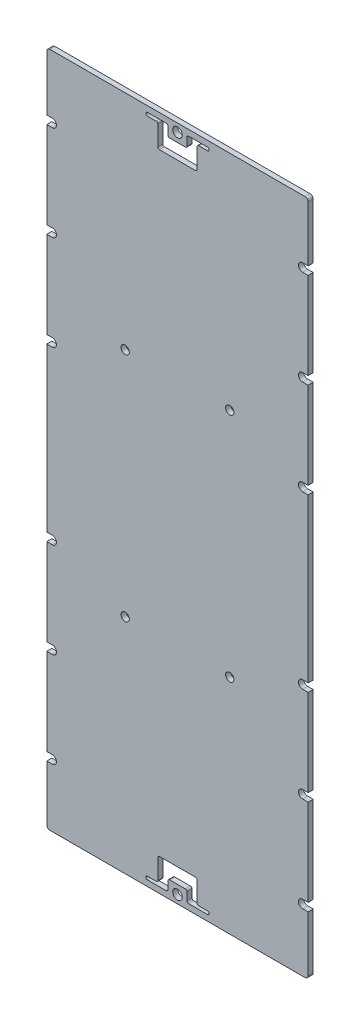
SolidWorks part; units mm, degrees
material "FR4_stuffedProtoboard"
ref_plane "Front Plane" through (0, 0, 0) normal (0, 0, 1) x (1, 0, 0)
ref_plane "Top Plane" through (0, 0, 0) normal (0, 1, 0) x (1, 0, 0)
ref_plane "Right Plane" through (0, 0, 0) normal (1, 0, 0) x (0, 0, -1)
sketch "Sketch1" plane through (0, 0, 0) normal (0, 0, 1) x (1, 0, 0)
  line L0 (-37, -97) -> (37, -97) construction
  line L5 (-37, -95.4) -> (37, -95.4) construction
  line L6 (-37, -87) -> (37, -87) construction
  line L7 (-37, -85.4) -> (37, -85.4) construction
  line L8 (-37, -77) -> (37, -77) construction
  line L9 (-37, -75.4) -> (37, -75.4) construction
  line L10 (-37, -67) -> (37, -67) construction
  line L11 (-37, -65.4) -> (37, -65.4) construction
  line L12 (-37, -57) -> (37, -57) construction
  line L13 (-37, -55.4) -> (37, -55.4) construction
  line L14 (-37, -47) -> (37, -47) construction
  line L15 (-37, -45.4) -> (37, -45.4) construction
  line L16 (-37, -37) -> (37, -37) construction
  line L17 (-37, -35.4) -> (37, -35.4) construction
  line L18 (-37, -27) -> (37, -27) construction
  line L19 (-37, -25.4) -> (37, -25.4) construction
  line L20 (-37, -17) -> (37, -17) construction
  line L21 (-37, -15.4) -> (37, -15.4) construction
  line L22 (-37, 15.4) -> (37, 15.4) construction
  line L23 (-37, 17) -> (37, 17) construction
  line L24 (-37, 25.4) -> (37, 25.4) construction
  line L25 (-37, 27) -> (37, 27) construction
  line L26 (-37, 35.4) -> (37, 35.4) construction
  line L27 (-37, 37) -> (37, 37) construction
  line L29 (-41.5, 107) -> (41.5, 107)
  line L30 (-41.5, 107) -> (-41.5, -107)
  line L31 (-41.5, -107) -> (41.5, -107)
  line L33 (41.5, 107) -> (41.5, -107)
  line L35 (-26.7, 107) -> (-28.3, 107) construction
  line L37 (-41.5, 109.5) -> (-41.5, 97.4) construction
  line L38 (41.5, 112.5) -> (41.5, 109.5) construction
  line L39 (-28.3, -107) -> (-26.7, -107) construction
  line L40 (-41.4, 106.9) -> (41.4, 106.9)
  line L41 (41.4, 106.9) -> (41.4, -106.9)
  line L42 (-41.4, -106.9) -> (41.4, -106.9)
  line L43 (-41.4, 106.9) -> (-41.4, -106.9)
  line L76 (-37, 45.4) -> (37, 45.4) construction
  line L77 (-37, 47) -> (37, 47) construction
  line L78 (-37, 55.4) -> (37, 55.4) construction
  line L79 (-37, 57) -> (37, 57) construction
  line L80 (-37, 65.4) -> (37, 65.4) construction
  line L81 (-37, 67) -> (37, 67) construction
  line L82 (-37, 75.4) -> (37, 75.4) construction
  line L83 (-37, 77) -> (37, 77) construction
  line L84 (-37, 85.4) -> (37, 85.4) construction
  line L85 (-37, 87) -> (37, 87) construction
  line L86 (-37, 95.4) -> (37, 95.4) construction
  line L87 (-37, 97) -> (37, 97) construction
  line L88 (-37, -97) -> (37, -97) construction
  line L89 (-37, -95.4) -> (37, -95.4) construction
  line L90 (-37, -87) -> (37, -87) construction
  line L91 (-37, -85.4) -> (37, -85.4) construction
  line L92 (-37, -77) -> (37, -77) construction
  line L93 (-37, -75.4) -> (37, -75.4) construction
  line L94 (-37, -67) -> (37, -67) construction
  line L95 (-37, -65.4) -> (37, -65.4) construction
  line L96 (-37, -57) -> (37, -57) construction
  line L97 (-37, -55.4) -> (37, -55.4) construction
  line L98 (-37, -47) -> (37, -47) construction
  line L99 (-37, -45.4) -> (37, -45.4) construction
  line L100 (-37, -37) -> (37, -37) construction
  line L101 (-37, -35.4) -> (37, -35.4) construction
  line L102 (-37, -27) -> (37, -27) construction
  line L103 (-37, -25.4) -> (37, -25.4) construction
  line L104 (-37, -17) -> (37, -17) construction
  line L105 (-37, -15.4) -> (37, -15.4) construction
  line L106 (-37, 15.4) -> (37, 15.4) construction
  line L107 (-37, 17) -> (37, 17) construction
  line L108 (-37, 25.4) -> (37, 25.4) construction
  line L109 (-37, 27) -> (37, 27) construction
  line L110 (-37, 35.4) -> (37, 35.4) construction
  line L111 (-37, 37) -> (37, 37) construction
  line L112 (-37, 45.4) -> (37, 45.4) construction
  line L113 (-37, 47) -> (37, 47) construction
  line L114 (-37, 55.4) -> (37, 55.4) construction
  line L115 (-37, 57) -> (37, 57) construction
  line L116 (-37, 65.4) -> (37, 65.4) construction
  line L117 (-37, 67) -> (37, 67) construction
  line L118 (-37, 75.4) -> (37, 75.4) construction
  line L119 (-37, 77) -> (37, 77) construction
  line L120 (-37, 85.4) -> (37, 85.4) construction
  line L121 (-37, 87) -> (37, 87) construction
  line L122 (-37, 95.4) -> (37, 95.4) construction
  line L123 (-37, 97) -> (37, 97) construction
  circle A0 centre (-39.5, 87) radius 0.8 construction
  circle A1 centre (-39.5, -27) radius 0.8 construction
  circle A2 centre (-39.5, 57) radius 0.8 construction
  circle A3 centre (39.5, -27) radius 0.8 construction
  circle A4 centre (-39.5, -27) radius 0.8
  circle A5 centre (-39.5, 27) radius 0.8 construction
  circle A6 centre (-16.5, 36.5) radius 0.8 construction
  circle A8 centre (39.5, -27) radius 0.8
  circle A9 centre (-16.5, -36.5) radius 0.8 construction
  circle A11 centre (-39.5, -57) radius 0.8 construction
  circle A13 centre (-39.5, -87) radius 0.8 construction
  circle A16 centre (0, -104.2) radius 0.8 construction
  circle A19 centre (39.5, -87) radius 0.8 construction
  circle A21 centre (39.5, -57) radius 0.8 construction
  circle A22 centre (16.5, -36.5) radius 0.8 construction
  circle A27 centre (39.5, 27) radius 0.8 construction
  circle A28 centre (16.5, 36.5) radius 0.8 construction
  circle A30 centre (39.5, 57) radius 0.8 construction
  circle A32 centre (39.5, 87) radius 0.8 construction
  circle A35 centre (0, 104.2) radius 0.8 construction
  circle A38 centre (-39.5, 87) radius 0.8
  circle A40 centre (-39.5, 57) radius 0.8
  circle A43 centre (-39.5, 27) radius 0.8
  circle A44 centre (-16.5, 36.5) radius 0.8
  circle A47 centre (-16.5, -36.5) radius 0.8
  circle A49 centre (-39.5, -57) radius 0.8
  circle A51 centre (-39.5, -87) radius 0.8
  circle A54 centre (0, -104.2) radius 0.8
  circle A57 centre (39.5, -87) radius 0.8
  circle A59 centre (39.5, -57) radius 0.8
  circle A60 centre (16.5, -36.5) radius 0.8
  circle A65 centre (39.5, 27) radius 0.8
  circle A66 centre (16.5, 36.5) radius 0.8
  circle A68 centre (39.5, 57) radius 0.8
  circle A70 centre (39.5, 87) radius 0.8
  circle A73 centre (0, 104.2) radius 0.8
  dimension "D1" = 0.1
extrude "pcb extrude" add sketch "Sketch1" along normal blind 1.6
sketch "Sketch7" plane through (0, 0, 1.6) normal (0, 0, 1) x (1, 0, 0)
  line L0 (-41.4, 106.9) -> (41.4, 106.9) construction
  line L1 (-41.25, 106.9) -> (-41.4, 106.9)
  line L2 (-41.25, 106.75) -> (-41.25, -106.75)
  line L3 (-41.25, -106.9) -> (-41.4, -106.9)
  line L4 (-41.4, 106.9) -> (-41.4, -106.9)
  line L5 (-41.4, -106.9) -> (41.4, -106.9) construction
  line L6 (-41.4, 106.9) -> (-41.4, -106.9) construction
  line L7 (0, -0.88) -> (0, 0.88) construction
  line L8 (41.25, -106.9) -> (41.4, -106.9)
  line L9 (41.4, 106.9) -> (41.4, -106.9)
  line L10 (41.25, 106.9) -> (41.4, 106.9)
  line L11 (41.25, 106.75) -> (41.25, -106.75)
  line L12 (0.88, 0) -> (-0.88, 0) construction
  line L13 (-41.25, -106.9) -> (41.25, -106.9)
  line L15 (-41.25, -106.75) -> (41.25, -106.75)
  line L17 (-41.25, 106.75) -> (41.25, 106.75)
  line L19 (-41.25, 106.9) -> (41.25, 106.9)
  dimension "D1" = 0.15
  dimension "D2" = 0.15
  dimension "D3" = 0.15
  dimension "D4" = 0.15
extrude "Offset Edges" cut sketch "Sketch7" against normal up to surface (1.6 mm away) up to face at (0.8, 104.2, 0)
sketch "connector locations" plane through (0, 0, 1.6) normal (0, 0, 1) x (1, 0, 0)
  line L0 (-37, 97) -> (37, 97) construction
  line L1 (-33.9182, 100.556) -> (-9.2802, 100.556)
  line L2 (-33.9182, 100.556) -> (-33.9182, 99.159)
  line L3 (-33.9182, 99.159) -> (-9.2802, 99.159)
  line L4 (-9.2802, 100.556) -> (-9.2802, 99.159)
  line L5 (-33.9182, 100.556) -> (-9.2802, 99.159) construction
  line L6 (-33.9182, 99.159) -> (-9.2802, 100.556) construction
  line L7 (-37, 87) -> (37, 87) construction
  line L8 (-33.9182, 90.556) -> (-22.0818, 90.556)
  line L9 (-33.9182, 90.556) -> (-33.9182, 89.159)
  line L10 (-33.9182, 89.159) -> (-22.0818, 89.159)
  line L11 (-22.0818, 90.556) -> (-22.0818, 89.159)
  line L12 (-33.9182, 90.556) -> (-22.0818, 89.159) construction
  line L13 (-33.9182, 89.159) -> (-22.0818, 90.556) construction
  line L14 (0, -0.88) -> (0, 0.88) construction
  line L15 (-12.319, 90.556) -> (12.319, 90.556)
  line L16 (-12.319, 90.556) -> (-12.319, 89.159)
  line L17 (-12.319, 89.159) -> (12.319, 89.159)
  line L18 (12.319, 90.556) -> (12.319, 89.159)
  line L19 (-12.319, 90.556) -> (12.319, 89.159) construction
  line L20 (-12.319, 89.159) -> (12.319, 90.556) construction
  line L21 (-37, -85.4) -> (37, -85.4) construction
  line L22 (-33.9182, -91.844) -> (-9.2802, -91.844)
  line L23 (-33.9182, -91.844) -> (-33.9182, -93.241)
  line L24 (-33.9182, -93.241) -> (-9.2802, -93.241)
  line L25 (-9.2802, -91.844) -> (-9.2802, -93.241)
  line L26 (-33.9182, -91.844) -> (-9.2802, -93.241) construction
  line L27 (-33.9182, -93.241) -> (-9.2802, -91.844) construction
  line L28 (-33.9182, -81.844) -> (-22.0818, -81.844)
  line L29 (-33.9182, -81.844) -> (-33.9182, -83.241)
  line L30 (-33.9182, -83.241) -> (-22.0818, -83.241)
  line L31 (-22.0818, -81.844) -> (-22.0818, -83.241)
  line L32 (-33.9182, -81.844) -> (-22.0818, -83.241) construction
  line L33 (-33.9182, -83.241) -> (-22.0818, -81.844) construction
  line L34 (-12.319, -81.844) -> (12.319, -81.844)
  line L35 (-12.319, -81.844) -> (-12.319, -83.241)
  line L36 (-12.319, -83.241) -> (12.319, -83.241)
  line L37 (12.319, -81.844) -> (12.319, -83.241)
  line L38 (-12.319, -81.844) -> (12.319, -83.241) construction
  line L39 (-12.319, -83.241) -> (12.319, -81.844) construction
  line L40 (-37, -95.4) -> (37, -95.4) construction
  line L41 (-33.9182, 80.556) -> (-33.9182, 79.159)
  line L42 (-33.9182, 80.556) -> (-22.0818, 80.556)
  line L43 (-22.0818, 80.556) -> (-22.0818, 79.159)
  line L44 (-33.9182, 79.159) -> (-22.0818, 79.159)
  line L45 (-33.9182, 80.556) -> (-22.0818, 79.159) construction
  line L46 (-33.9182, 79.159) -> (-22.0818, 80.556) construction
  line L47 (-12.319, 80.556) -> (-12.319, 79.159)
  line L48 (-12.319, 80.556) -> (12.319, 80.556)
  line L49 (12.319, 80.556) -> (12.319, 79.159)
  line L50 (-12.319, 79.159) -> (12.319, 79.159)
  line L51 (-12.319, 80.556) -> (12.319, 79.159) construction
  line L52 (-12.319, 79.159) -> (12.319, 80.556) construction
  line L53 (-33.9182, 70.556) -> (-33.9182, 69.159)
  line L54 (-33.9182, 70.556) -> (-22.0818, 70.556)
  line L55 (-22.0818, 70.556) -> (-22.0818, 69.159)
  line L56 (-33.9182, 69.159) -> (-22.0818, 69.159)
  line L57 (-33.9182, 70.556) -> (-22.0818, 69.159) construction
  line L58 (-33.9182, 69.159) -> (-22.0818, 70.556) construction
  line L59 (-12.319, 70.556) -> (-12.319, 69.159)
  line L60 (-12.319, 70.556) -> (12.319, 70.556)
  line L61 (12.319, 70.556) -> (12.319, 69.159)
  line L62 (-12.319, 69.159) -> (12.319, 69.159)
  line L63 (-12.319, 70.556) -> (12.319, 69.159) construction
  line L64 (-12.319, 69.159) -> (12.319, 70.556) construction
  line L65 (-33.9182, 60.556) -> (-33.9182, 59.159)
  line L66 (-33.9182, 60.556) -> (-22.0818, 60.556)
  line L67 (-22.0818, 60.556) -> (-22.0818, 59.159)
  line L68 (-33.9182, 59.159) -> (-22.0818, 59.159)
  line L69 (-33.9182, 60.556) -> (-22.0818, 59.159) construction
  line L70 (-33.9182, 59.159) -> (-22.0818, 60.556) construction
  line L71 (-12.319, 60.556) -> (-12.319, 59.159)
  line L72 (-12.319, 60.556) -> (12.319, 60.556)
  line L73 (12.319, 60.556) -> (12.319, 59.159)
  line L74 (-12.319, 59.159) -> (12.319, 59.159)
  line L75 (-12.319, 60.556) -> (12.319, 59.159) construction
  line L76 (-12.319, 59.159) -> (12.319, 60.556) construction
  line L77 (-33.9182, 50.556) -> (-33.9182, 49.159)
  line L78 (-33.9182, 50.556) -> (-22.0818, 50.556)
  line L79 (-22.0818, 50.556) -> (-22.0818, 49.159)
  line L80 (-33.9182, 49.159) -> (-22.0818, 49.159)
  line L81 (-33.9182, 50.556) -> (-22.0818, 49.159) construction
  line L82 (-33.9182, 49.159) -> (-22.0818, 50.556) construction
  line L83 (-12.319, 50.556) -> (-12.319, 49.159)
  line L84 (-12.319, 50.556) -> (12.319, 50.556)
  line L85 (12.319, 50.556) -> (12.319, 49.159)
  line L86 (-12.319, 49.159) -> (12.319, 49.159)
  line L87 (-12.319, 50.556) -> (12.319, 49.159) construction
  line L88 (-12.319, 49.159) -> (12.319, 50.556) construction
  line L89 (-33.9182, 40.556) -> (-33.9182, 39.159)
  line L90 (-33.9182, 40.556) -> (-22.0818, 40.556)
  line L91 (-22.0818, 40.556) -> (-22.0818, 39.159)
  line L92 (-33.9182, 39.159) -> (-22.0818, 39.159)
  line L93 (-33.9182, 40.556) -> (-22.0818, 39.159) construction
  line L94 (-33.9182, 39.159) -> (-22.0818, 40.556) construction
  line L95 (-12.319, 40.556) -> (-12.319, 39.159)
  line L96 (-12.319, 40.556) -> (12.319, 40.556)
  line L97 (12.319, 40.556) -> (12.319, 39.159)
  line L98 (-12.319, 39.159) -> (12.319, 39.159)
  line L99 (-12.319, 40.556) -> (12.319, 39.159) construction
  line L100 (-12.319, 39.159) -> (12.319, 40.556) construction
  line L101 (-33.9182, 30.556) -> (-33.9182, 29.159)
  line L102 (-33.9182, 30.556) -> (-22.0818, 30.556)
  line L103 (-22.0818, 30.556) -> (-22.0818, 29.159)
  line L104 (-33.9182, 29.159) -> (-22.0818, 29.159)
  line L105 (-33.9182, 30.556) -> (-22.0818, 29.159) construction
  line L106 (-33.9182, 29.159) -> (-22.0818, 30.556) construction
  line L107 (-12.319, 30.556) -> (-12.319, 29.159)
  line L108 (-12.319, 30.556) -> (12.319, 30.556)
  line L109 (12.319, 30.556) -> (12.319, 29.159)
  line L110 (-12.319, 29.159) -> (12.319, 29.159)
  line L111 (-12.319, 30.556) -> (12.319, 29.159) construction
  line L112 (-12.319, 29.159) -> (12.319, 30.556) construction
  line L113 (-33.9182, 20.556) -> (-33.9182, 19.159)
  line L114 (-33.9182, 20.556) -> (-22.0818, 20.556)
  line L115 (-22.0818, 20.556) -> (-22.0818, 19.159)
  line L116 (-33.9182, 19.159) -> (-22.0818, 19.159)
  line L117 (-33.9182, 20.556) -> (-22.0818, 19.159) construction
  line L118 (-33.9182, 19.159) -> (-22.0818, 20.556) construction
  line L119 (-12.319, 20.556) -> (-12.319, 19.159)
  line L120 (-12.319, 20.556) -> (12.319, 20.556)
  line L121 (12.319, 20.556) -> (12.319, 19.159)
  line L122 (-12.319, 19.159) -> (12.319, 19.159)
  line L123 (-12.319, 20.556) -> (12.319, 19.159) construction
  line L124 (-12.319, 19.159) -> (12.319, 20.556) construction
  line L125 (-33.9182, 10.556) -> (-33.9182, 9.159)
  line L126 (-33.9182, 10.556) -> (-22.0818, 10.556)
  line L127 (-22.0818, 10.556) -> (-22.0818, 9.159)
  line L128 (-33.9182, 9.159) -> (-22.0818, 9.159)
  line L129 (-33.9182, 10.556) -> (-22.0818, 9.159) construction
  line L130 (-33.9182, 9.159) -> (-22.0818, 10.556) construction
  line L131 (-12.319, 10.556) -> (-12.319, 9.159)
  line L132 (-12.319, 10.556) -> (12.319, 10.556)
  line L133 (12.319, 10.556) -> (12.319, 9.159)
  line L134 (-12.319, 9.159) -> (12.319, 9.159)
  line L135 (-12.319, 10.556) -> (12.319, 9.159) construction
  line L136 (-12.319, 9.159) -> (12.319, 10.556) construction
  line L137 (0, 89.8575) -> (0, 79.8575) construction
  line L138 (-33.9182, -71.844) -> (-33.9182, -73.241)
  line L139 (-33.9182, -71.844) -> (-22.0818, -71.844)
  line L140 (-22.0818, -71.844) -> (-22.0818, -73.241)
  line L141 (-33.9182, -73.241) -> (-22.0818, -73.241)
  line L142 (-33.9182, -73.241) -> (-22.0818, -71.844) construction
  line L143 (-33.9182, -71.844) -> (-22.0818, -73.241) construction
  line L144 (-12.319, -71.844) -> (-12.319, -73.241)
  line L145 (-12.319, -71.844) -> (12.319, -71.844)
  line L146 (12.319, -71.844) -> (12.319, -73.241)
  line L147 (-12.319, -73.241) -> (12.319, -73.241)
  line L148 (-12.319, -73.241) -> (12.319, -71.844) construction
  line L149 (-12.319, -71.844) -> (12.319, -73.241) construction
  line L150 (-33.9182, -61.844) -> (-33.9182, -63.241)
  line L151 (-33.9182, -61.844) -> (-22.0818, -61.844)
  line L152 (-22.0818, -61.844) -> (-22.0818, -63.241)
  line L153 (-33.9182, -63.241) -> (-22.0818, -63.241)
  line L154 (-33.9182, -63.241) -> (-22.0818, -61.844) construction
  line L155 (-33.9182, -61.844) -> (-22.0818, -63.241) construction
  line L156 (-12.319, -61.844) -> (-12.319, -63.241)
  line L157 (-12.319, -61.844) -> (12.319, -61.844)
  line L158 (12.319, -61.844) -> (12.319, -63.241)
  line L159 (-12.319, -63.241) -> (12.319, -63.241)
  line L160 (-12.319, -63.241) -> (12.319, -61.844) construction
  line L161 (-12.319, -61.844) -> (12.319, -63.241) construction
  line L162 (-33.9182, -51.844) -> (-33.9182, -53.241)
  line L163 (-33.9182, -51.844) -> (-22.0818, -51.844)
  line L164 (-22.0818, -51.844) -> (-22.0818, -53.241)
  line L165 (-33.9182, -53.241) -> (-22.0818, -53.241)
  line L166 (-33.9182, -53.241) -> (-22.0818, -51.844) construction
  line L167 (-33.9182, -51.844) -> (-22.0818, -53.241) construction
  line L168 (-12.319, -51.844) -> (-12.319, -53.241)
  line L169 (-12.319, -51.844) -> (12.319, -51.844)
  line L170 (12.319, -51.844) -> (12.319, -53.241)
  line L171 (-12.319, -53.241) -> (12.319, -53.241)
  line L172 (-12.319, -53.241) -> (12.319, -51.844) construction
  line L173 (-12.319, -51.844) -> (12.319, -53.241) construction
  line L174 (-33.9182, -41.844) -> (-33.9182, -43.241)
  line L175 (-33.9182, -41.844) -> (-22.0818, -41.844)
  line L176 (-22.0818, -41.844) -> (-22.0818, -43.241)
  line L177 (-33.9182, -43.241) -> (-22.0818, -43.241)
  line L178 (-33.9182, -43.241) -> (-22.0818, -41.844) construction
  line L179 (-33.9182, -41.844) -> (-22.0818, -43.241) construction
  line L180 (-12.319, -41.844) -> (-12.319, -43.241)
  line L181 (-12.319, -41.844) -> (12.319, -41.844)
  line L182 (12.319, -41.844) -> (12.319, -43.241)
  line L183 (-12.319, -43.241) -> (12.319, -43.241)
  line L184 (-12.319, -43.241) -> (12.319, -41.844) construction
  line L185 (-12.319, -41.844) -> (12.319, -43.241) construction
  line L186 (-33.9182, -31.844) -> (-33.9182, -33.241)
  line L187 (-33.9182, -31.844) -> (-22.0818, -31.844)
  line L188 (-22.0818, -31.844) -> (-22.0818, -33.241)
  line L189 (-33.9182, -33.241) -> (-22.0818, -33.241)
  line L190 (-33.9182, -33.241) -> (-22.0818, -31.844) construction
  line L191 (-33.9182, -31.844) -> (-22.0818, -33.241) construction
  line L192 (-12.319, -31.844) -> (-12.319, -33.241)
  line L193 (-12.319, -31.844) -> (12.319, -31.844)
  line L194 (12.319, -31.844) -> (12.319, -33.241)
  line L195 (-12.319, -33.241) -> (12.319, -33.241)
  line L196 (-12.319, -33.241) -> (12.319, -31.844) construction
  line L197 (-12.319, -31.844) -> (12.319, -33.241) construction
  line L198 (-33.9182, -21.844) -> (-33.9182, -23.241)
  line L199 (-33.9182, -21.844) -> (-22.0818, -21.844)
  line L200 (-22.0818, -21.844) -> (-22.0818, -23.241)
  line L201 (-33.9182, -23.241) -> (-22.0818, -23.241)
  line L202 (-33.9182, -23.241) -> (-22.0818, -21.844) construction
  line L203 (-33.9182, -21.844) -> (-22.0818, -23.241) construction
  line L204 (-12.319, -21.844) -> (-12.319, -23.241)
  line L205 (-12.319, -21.844) -> (12.319, -21.844)
  line L206 (12.319, -21.844) -> (12.319, -23.241)
  line L207 (-12.319, -23.241) -> (12.319, -23.241)
  line L208 (-12.319, -23.241) -> (12.319, -21.844) construction
  line L209 (-12.319, -21.844) -> (12.319, -23.241) construction
  line L210 (-33.9182, -11.844) -> (-33.9182, -13.241)
  line L211 (-33.9182, -11.844) -> (-22.0818, -11.844)
  line L212 (-22.0818, -11.844) -> (-22.0818, -13.241)
  line L213 (-33.9182, -13.241) -> (-22.0818, -13.241)
  line L214 (-33.9182, -13.241) -> (-22.0818, -11.844) construction
  line L215 (-33.9182, -11.844) -> (-22.0818, -13.241) construction
  line L216 (-12.319, -11.844) -> (-12.319, -13.241)
  line L217 (-12.319, -11.844) -> (12.319, -11.844)
  line L218 (12.319, -11.844) -> (12.319, -13.241)
  line L219 (-12.319, -13.241) -> (12.319, -13.241)
  line L220 (-12.319, -13.241) -> (12.319, -11.844) construction
  line L221 (-12.319, -11.844) -> (12.319, -13.241) construction
  line L222 (-33.9182, -1.844) -> (-33.9182, -3.241)
  line L223 (-33.9182, -1.844) -> (-22.0818, -1.844)
  line L224 (-22.0818, -1.844) -> (-22.0818, -3.241)
  line L225 (-33.9182, -3.241) -> (-22.0818, -3.241)
  line L226 (-33.9182, -3.241) -> (-22.0818, -1.844) construction
  line L227 (-33.9182, -1.844) -> (-22.0818, -3.241) construction
  line L228 (-12.319, -1.844) -> (-12.319, -3.241)
  line L229 (-12.319, -1.844) -> (12.319, -1.844)
  line L230 (12.319, -1.844) -> (12.319, -3.241)
  line L231 (-12.319, -3.241) -> (12.319, -3.241)
  line L232 (-12.319, -3.241) -> (12.319, -1.844) construction
  line L233 (-12.319, -1.844) -> (12.319, -3.241) construction
  line L234 (0, -82.5425) -> (0, -72.5425) construction
  line L235 (26.92, 96.39) -> (29.08, 98.57) construction
  line L236 (26.92, 98.57) -> (29.08, 96.39) construction
  line L237 (32.92, 98.57) -> (35.08, 96.39) construction
  line L238 (32.92, 96.39) -> (35.08, 98.57) construction
  line L239 (20.92, 96.39) -> (23.08, 98.57) construction
  line L240 (20.92, 98.57) -> (23.08, 96.39) construction
  line L241 (26.92, 86.39) -> (29.08, 88.57) construction
  line L242 (26.92, 88.57) -> (29.08, 86.39) construction
  line L243 (20.92, 86.39) -> (23.08, 88.57) construction
  line L244 (20.92, 88.57) -> (23.08, 86.39) construction
  line L245 (26.92, 76.39) -> (29.08, 78.57) construction
  line L246 (26.92, 78.57) -> (29.08, 76.39) construction
  line L247 (20.92, 76.39) -> (23.08, 78.57) construction
  line L248 (20.92, 78.57) -> (23.08, 76.39) construction
  line L249 (26.92, 66.39) -> (29.08, 68.57) construction
  line L250 (26.92, 68.57) -> (29.08, 66.39) construction
  line L251 (20.92, 66.39) -> (23.08, 68.57) construction
  line L252 (20.92, 68.57) -> (23.08, 66.39) construction
  line L253 (26.92, 56.39) -> (29.08, 58.57) construction
  line L254 (26.92, 58.57) -> (29.08, 56.39) construction
  line L255 (20.92, 56.39) -> (23.08, 58.57) construction
  line L256 (20.92, 58.57) -> (23.08, 56.39) construction
  line L257 (26.92, 46.39) -> (29.08, 48.57) construction
  line L258 (26.92, 48.57) -> (29.08, 46.39) construction
  line L259 (20.92, 46.39) -> (23.08, 48.57) construction
  line L260 (20.92, 48.57) -> (23.08, 46.39) construction
  line L261 (26.92, 36.39) -> (29.08, 38.57) construction
  line L262 (26.92, 38.57) -> (29.08, 36.39) construction
  line L263 (20.92, 36.39) -> (23.08, 38.57) construction
  line L264 (20.92, 38.57) -> (23.08, 36.39) construction
  line L265 (26.92, 26.39) -> (29.08, 28.57) construction
  line L266 (26.92, 28.57) -> (29.08, 26.39) construction
  line L267 (20.92, 26.39) -> (23.08, 28.57) construction
  line L268 (20.92, 28.57) -> (23.08, 26.39) construction
  line L269 (26.92, 16.39) -> (29.08, 18.57) construction
  line L270 (26.92, 18.57) -> (29.08, 16.39) construction
  line L271 (20.92, 16.39) -> (23.08, 18.57) construction
  line L272 (20.92, 18.57) -> (23.08, 16.39) construction
  line L273 (26.92, 6.39) -> (29.08, 8.57) construction
  line L274 (26.92, 8.57) -> (29.08, 6.39) construction
  line L275 (20.92, 6.39) -> (23.08, 8.57) construction
  line L276 (20.92, 8.57) -> (23.08, 6.39) construction
  line L277 (32.92, 86.39) -> (35.08, 88.57) construction
  line L278 (32.92, 88.57) -> (35.08, 86.39) construction
  line L279 (32.92, 76.39) -> (35.08, 78.57) construction
  line L280 (32.92, 78.57) -> (35.08, 76.39) construction
  line L281 (32.92, 66.39) -> (35.08, 68.57) construction
  line L282 (32.92, 68.57) -> (35.08, 66.39) construction
  line L283 (32.92, 56.39) -> (35.08, 58.57) construction
  line L284 (32.92, 58.57) -> (35.08, 56.39) construction
  line L285 (32.92, 46.39) -> (35.08, 48.57) construction
  line L286 (32.92, 48.57) -> (35.08, 46.39) construction
  line L287 (32.92, 36.39) -> (35.08, 38.57) construction
  line L288 (32.92, 38.57) -> (35.08, 36.39) construction
  line L289 (32.92, 26.39) -> (35.08, 28.57) construction
  line L290 (32.92, 28.57) -> (35.08, 26.39) construction
  line L291 (32.92, 16.39) -> (35.08, 18.57) construction
  line L292 (32.92, 18.57) -> (35.08, 16.39) construction
  line L293 (32.92, 6.39) -> (35.08, 8.57) construction
  line L294 (32.92, 8.57) -> (35.08, 6.39) construction
  line L295 (32.92, 98.57) -> (26.92, 98.57) construction
  line L296 (32.92, 98.57) -> (32.92, 88.57) construction
  line L297 (32.92, -93.83) -> (35.08, -96.01) construction
  line L298 (35.08, -93.83) -> (32.92, -96.01) construction
  line L299 (29.08, -93.83) -> (26.92, -96.01) construction
  line L300 (26.92, -93.83) -> (29.08, -96.01) construction
  line L301 (23.08, -93.83) -> (20.92, -96.01) construction
  line L302 (20.92, -93.83) -> (23.08, -96.01) construction
  line L303 (29.08, -83.83) -> (26.92, -86.01) construction
  line L304 (26.92, -83.83) -> (29.08, -86.01) construction
  line L305 (23.08, -83.83) -> (20.92, -86.01) construction
  line L306 (20.92, -83.83) -> (23.08, -86.01) construction
  line L307 (29.08, -73.83) -> (26.92, -76.01) construction
  line L308 (26.92, -73.83) -> (29.08, -76.01) construction
  line L309 (23.08, -73.83) -> (20.92, -76.01) construction
  line L310 (20.92, -73.83) -> (23.08, -76.01) construction
  line L311 (29.08, -63.83) -> (26.92, -66.01) construction
  line L312 (26.92, -63.83) -> (29.08, -66.01) construction
  line L313 (23.08, -63.83) -> (20.92, -66.01) construction
  line L314 (20.92, -63.83) -> (23.08, -66.01) construction
  line L315 (29.08, -53.83) -> (26.92, -56.01) construction
  line L316 (26.92, -53.83) -> (29.08, -56.01) construction
  line L317 (23.08, -53.83) -> (20.92, -56.01) construction
  line L318 (20.92, -53.83) -> (23.08, -56.01) construction
  line L319 (29.08, -43.83) -> (26.92, -46.01) construction
  line L320 (26.92, -43.83) -> (29.08, -46.01) construction
  line L321 (23.08, -43.83) -> (20.92, -46.01) construction
  line L322 (20.92, -43.83) -> (23.08, -46.01) construction
  line L323 (29.08, -33.83) -> (26.92, -36.01) construction
  line L324 (26.92, -33.83) -> (29.08, -36.01) construction
  line L325 (23.08, -33.83) -> (20.92, -36.01) construction
  line L326 (20.92, -33.83) -> (23.08, -36.01) construction
  line L327 (29.08, -23.83) -> (26.92, -26.01) construction
  line L328 (26.92, -23.83) -> (29.08, -26.01) construction
  line L329 (23.08, -23.83) -> (20.92, -26.01) construction
  line L330 (20.92, -23.83) -> (23.08, -26.01) construction
  line L331 (29.08, -13.83) -> (26.92, -16.01) construction
  line L332 (26.92, -13.83) -> (29.08, -16.01) construction
  line L333 (23.08, -13.83) -> (20.92, -16.01) construction
  line L334 (20.92, -13.83) -> (23.08, -16.01) construction
  line L335 (29.08, -3.83) -> (26.92, -6.01) construction
  line L336 (26.92, -3.83) -> (29.08, -6.01) construction
  line L337 (23.08, -3.83) -> (20.92, -6.01) construction
  line L338 (20.92, -3.83) -> (23.08, -6.01) construction
  line L339 (35.08, -83.83) -> (32.92, -86.01) construction
  line L340 (32.92, -83.83) -> (35.08, -86.01) construction
  line L341 (35.08, -73.83) -> (32.92, -76.01) construction
  line L342 (32.92, -73.83) -> (35.08, -76.01) construction
  line L343 (35.08, -63.83) -> (32.92, -66.01) construction
  line L344 (32.92, -63.83) -> (35.08, -66.01) construction
  line L345 (35.08, -53.83) -> (32.92, -56.01) construction
  line L346 (32.92, -53.83) -> (35.08, -56.01) construction
  line L347 (35.08, -43.83) -> (32.92, -46.01) construction
  line L348 (32.92, -43.83) -> (35.08, -46.01) construction
  line L349 (35.08, -33.83) -> (32.92, -36.01) construction
  line L350 (32.92, -33.83) -> (35.08, -36.01) construction
  line L351 (35.08, -23.83) -> (32.92, -26.01) construction
  line L352 (32.92, -23.83) -> (35.08, -26.01) construction
  line L353 (35.08, -13.83) -> (32.92, -16.01) construction
  line L354 (32.92, -13.83) -> (35.08, -16.01) construction
  line L355 (35.08, -3.83) -> (32.92, -6.01) construction
  line L356 (32.92, -3.83) -> (35.08, -6.01) construction
  line L357 (32.92, -93.83) -> (26.92, -93.83) construction
  line L358 (32.92, -93.83) -> (32.92, -83.83) construction
  line L359 (-28, 89.8575) -> (-28, 79.8575) construction
  line L360 (-28, -82.5425) -> (-28, -72.5425) construction
  line L361 (-37, 100.5) -> (-37, -100.5) construction
  line L362 (-34.5, -103) -> (-4.5, -103) construction
  line L363 (-2.5, -102) -> (2.5, -102) construction
  line L364 (4.5, -103) -> (34.5, -103) construction
  line L365 (37, -100.5) -> (37, 100.5) construction
  line L366 (34.5, 103) -> (4.5, 103) construction
  line L367 (-2.5, 102) -> (2.5, 102) construction
  line L368 (-4.5, 103) -> (-34.5, 103) construction
  line L369 (-37, 100.5) -> (-37, -100.5)
  line L370 (-34.5, -103) -> (-4.5, -103)
  line L371 (-2.5, -102) -> (2.5, -102)
  line L372 (4.5, -103) -> (34.5, -103)
  line L373 (37, -100.5) -> (37, 100.5)
  line L374 (34.5, 103) -> (4.5, 103)
  line L375 (-2.5, 102) -> (2.5, 102)
  line L376 (-4.5, 103) -> (-34.5, 103)
  circle A0 centre (32.92, 98.57) radius 0.32
  circle A1 centre (35.08, 98.57) radius 0.32
  circle A2 centre (35.08, 96.39) radius 0.32
  circle A3 centre (32.92, 96.39) radius 0.32
  circle A4 centre (26.92, 98.57) radius 0.32
  circle A5 centre (29.08, 98.57) radius 0.32
  circle A6 centre (29.08, 96.39) radius 0.32
  circle A7 centre (26.92, 96.39) radius 0.32
  circle A8 centre (20.92, 98.57) radius 0.32
  circle A9 centre (23.08, 98.57) radius 0.32
  circle A10 centre (23.08, 96.39) radius 0.32
  circle A11 centre (20.92, 96.39) radius 0.32
  circle A12 centre (26.92, 88.57) radius 0.32
  circle A13 centre (29.08, 88.57) radius 0.32
  circle A14 centre (29.08, 86.39) radius 0.32
  circle A15 centre (26.92, 86.39) radius 0.32
  circle A16 centre (20.92, 88.57) radius 0.32
  circle A17 centre (23.08, 88.57) radius 0.32
  circle A18 centre (23.08, 86.39) radius 0.32
  circle A19 centre (20.92, 86.39) radius 0.32
  circle A20 centre (26.92, 78.57) radius 0.32
  circle A21 centre (29.08, 78.57) radius 0.32
  circle A22 centre (29.08, 76.39) radius 0.32
  circle A23 centre (26.92, 76.39) radius 0.32
  circle A24 centre (20.92, 78.57) radius 0.32
  circle A25 centre (23.08, 78.57) radius 0.32
  circle A26 centre (23.08, 76.39) radius 0.32
  circle A27 centre (20.92, 76.39) radius 0.32
  circle A28 centre (26.92, 68.57) radius 0.32
  circle A29 centre (29.08, 68.57) radius 0.32
  circle A30 centre (29.08, 66.39) radius 0.32
  circle A31 centre (26.92, 66.39) radius 0.32
  circle A32 centre (20.92, 68.57) radius 0.32
  circle A33 centre (23.08, 68.57) radius 0.32
  circle A34 centre (23.08, 66.39) radius 0.32
  circle A35 centre (20.92, 66.39) radius 0.32
  circle A36 centre (26.92, 58.57) radius 0.32
  circle A37 centre (29.08, 58.57) radius 0.32
  circle A38 centre (29.08, 56.39) radius 0.32
  circle A39 centre (26.92, 56.39) radius 0.32
  circle A40 centre (20.92, 58.57) radius 0.32
  circle A41 centre (23.08, 58.57) radius 0.32
  circle A42 centre (23.08, 56.39) radius 0.32
  circle A43 centre (20.92, 56.39) radius 0.32
  circle A44 centre (26.92, 48.57) radius 0.32
  circle A45 centre (29.08, 48.57) radius 0.32
  circle A46 centre (29.08, 46.39) radius 0.32
  circle A47 centre (26.92, 46.39) radius 0.32
  circle A48 centre (20.92, 48.57) radius 0.32
  circle A49 centre (23.08, 48.57) radius 0.32
  circle A50 centre (23.08, 46.39) radius 0.32
  circle A51 centre (20.92, 46.39) radius 0.32
  circle A52 centre (26.92, 38.57) radius 0.32
  circle A53 centre (29.08, 38.57) radius 0.32
  circle A54 centre (29.08, 36.39) radius 0.32
  circle A55 centre (26.92, 36.39) radius 0.32
  circle A56 centre (20.92, 38.57) radius 0.32
  circle A57 centre (23.08, 38.57) radius 0.32
  circle A58 centre (23.08, 36.39) radius 0.32
  circle A59 centre (20.92, 36.39) radius 0.32
  circle A60 centre (26.92, 28.57) radius 0.32
  circle A61 centre (29.08, 28.57) radius 0.32
  circle A62 centre (29.08, 26.39) radius 0.32
  circle A63 centre (26.92, 26.39) radius 0.32
  circle A64 centre (20.92, 28.57) radius 0.32
  circle A65 centre (23.08, 28.57) radius 0.32
  circle A66 centre (23.08, 26.39) radius 0.32
  circle A67 centre (20.92, 26.39) radius 0.32
  circle A68 centre (26.92, 18.57) radius 0.32
  circle A69 centre (29.08, 18.57) radius 0.32
  circle A70 centre (29.08, 16.39) radius 0.32
  circle A71 centre (26.92, 16.39) radius 0.32
  circle A72 centre (20.92, 18.57) radius 0.32
  circle A73 centre (23.08, 18.57) radius 0.32
  circle A74 centre (23.08, 16.39) radius 0.32
  circle A75 centre (20.92, 16.39) radius 0.32
  circle A76 centre (26.92, 8.57) radius 0.32
  circle A77 centre (29.08, 8.57) radius 0.32
  circle A78 centre (29.08, 6.39) radius 0.32
  circle A79 centre (26.92, 6.39) radius 0.32
  circle A80 centre (20.92, 8.57) radius 0.32
  circle A81 centre (23.08, 8.57) radius 0.32
  circle A82 centre (23.08, 6.39) radius 0.32
  circle A83 centre (20.92, 6.39) radius 0.32
  circle A84 centre (32.92, 88.57) radius 0.32
  circle A85 centre (35.08, 88.57) radius 0.32
  circle A86 centre (35.08, 86.39) radius 0.32
  circle A87 centre (32.92, 86.39) radius 0.32
  circle A88 centre (32.92, 78.57) radius 0.32
  circle A89 centre (35.08, 78.57) radius 0.32
  circle A90 centre (35.08, 76.39) radius 0.32
  circle A91 centre (32.92, 76.39) radius 0.32
  circle A92 centre (32.92, 68.57) radius 0.32
  circle A93 centre (35.08, 68.57) radius 0.32
  circle A94 centre (35.08, 66.39) radius 0.32
  circle A95 centre (32.92, 66.39) radius 0.32
  circle A96 centre (32.92, 58.57) radius 0.32
  circle A97 centre (35.08, 58.57) radius 0.32
  circle A98 centre (35.08, 56.39) radius 0.32
  circle A99 centre (32.92, 56.39) radius 0.32
  circle A100 centre (32.92, 48.57) radius 0.32
  circle A101 centre (35.08, 48.57) radius 0.32
  circle A102 centre (35.08, 46.39) radius 0.32
  circle A103 centre (32.92, 46.39) radius 0.32
  circle A104 centre (32.92, 38.57) radius 0.32
  circle A105 centre (35.08, 38.57) radius 0.32
  circle A106 centre (35.08, 36.39) radius 0.32
  circle A107 centre (32.92, 36.39) radius 0.32
  circle A108 centre (32.92, 28.57) radius 0.32
  circle A109 centre (35.08, 28.57) radius 0.32
  circle A110 centre (35.08, 26.39) radius 0.32
  circle A111 centre (32.92, 26.39) radius 0.32
  circle A112 centre (32.92, 18.57) radius 0.32
  circle A113 centre (35.08, 18.57) radius 0.32
  circle A114 centre (35.08, 16.39) radius 0.32
  circle A115 centre (32.92, 16.39) radius 0.32
  circle A116 centre (32.92, 8.57) radius 0.32
  circle A117 centre (35.08, 8.57) radius 0.32
  circle A118 centre (35.08, 6.39) radius 0.32
  circle A119 centre (32.92, 6.39) radius 0.32
  circle A120 centre (35.08, -93.83) radius 0.32
  circle A121 centre (32.92, -93.83) radius 0.32
  circle A122 centre (32.92, -96.01) radius 0.32
  circle A123 centre (35.08, -96.01) radius 0.32
  circle A124 centre (26.92, -93.83) radius 0.32
  circle A125 centre (29.08, -93.83) radius 0.32
  circle A126 centre (29.08, -96.01) radius 0.32
  circle A127 centre (26.92, -96.01) radius 0.32
  circle A128 centre (20.92, -93.83) radius 0.32
  circle A129 centre (23.08, -93.83) radius 0.32
  circle A130 centre (23.08, -96.01) radius 0.32
  circle A131 centre (20.92, -96.01) radius 0.32
  circle A132 centre (26.92, -83.83) radius 0.32
  circle A133 centre (29.08, -83.83) radius 0.32
  circle A134 centre (29.08, -86.01) radius 0.32
  circle A135 centre (26.92, -86.01) radius 0.32
  circle A136 centre (20.92, -83.83) radius 0.32
  circle A137 centre (23.08, -83.83) radius 0.32
  circle A138 centre (23.08, -86.01) radius 0.32
  circle A139 centre (20.92, -86.01) radius 0.32
  circle A140 centre (26.92, -73.83) radius 0.32
  circle A141 centre (29.08, -73.83) radius 0.32
  circle A142 centre (29.08, -76.01) radius 0.32
  circle A143 centre (26.92, -76.01) radius 0.32
  circle A144 centre (20.92, -73.83) radius 0.32
  circle A145 centre (23.08, -73.83) radius 0.32
  circle A146 centre (23.08, -76.01) radius 0.32
  circle A147 centre (20.92, -76.01) radius 0.32
  circle A148 centre (26.92, -63.83) radius 0.32
  circle A149 centre (29.08, -63.83) radius 0.32
  circle A150 centre (29.08, -66.01) radius 0.32
  circle A151 centre (26.92, -66.01) radius 0.32
  circle A152 centre (20.92, -63.83) radius 0.32
  circle A153 centre (23.08, -63.83) radius 0.32
  circle A154 centre (23.08, -66.01) radius 0.32
  circle A155 centre (20.92, -66.01) radius 0.32
  circle A156 centre (26.92, -53.83) radius 0.32
  circle A157 centre (29.08, -53.83) radius 0.32
  circle A158 centre (29.08, -56.01) radius 0.32
  circle A159 centre (26.92, -56.01) radius 0.32
  circle A160 centre (20.92, -53.83) radius 0.32
  circle A161 centre (23.08, -53.83) radius 0.32
  circle A162 centre (23.08, -56.01) radius 0.32
  circle A163 centre (20.92, -56.01) radius 0.32
  circle A164 centre (26.92, -43.83) radius 0.32
  circle A165 centre (29.08, -43.83) radius 0.32
  circle A166 centre (29.08, -46.01) radius 0.32
  circle A167 centre (26.92, -46.01) radius 0.32
  circle A168 centre (20.92, -43.83) radius 0.32
  circle A169 centre (23.08, -43.83) radius 0.32
  circle A170 centre (23.08, -46.01) radius 0.32
  circle A171 centre (20.92, -46.01) radius 0.32
  circle A172 centre (26.92, -33.83) radius 0.32
  circle A173 centre (29.08, -33.83) radius 0.32
  circle A174 centre (29.08, -36.01) radius 0.32
  circle A175 centre (26.92, -36.01) radius 0.32
  circle A176 centre (20.92, -33.83) radius 0.32
  circle A177 centre (23.08, -33.83) radius 0.32
  circle A178 centre (23.08, -36.01) radius 0.32
  circle A179 centre (20.92, -36.01) radius 0.32
  circle A180 centre (26.92, -23.83) radius 0.32
  circle A181 centre (29.08, -23.83) radius 0.32
  circle A182 centre (29.08, -26.01) radius 0.32
  circle A183 centre (26.92, -26.01) radius 0.32
  circle A184 centre (20.92, -23.83) radius 0.32
  circle A185 centre (23.08, -23.83) radius 0.32
  circle A186 centre (23.08, -26.01) radius 0.32
  circle A187 centre (20.92, -26.01) radius 0.32
  circle A188 centre (26.92, -13.83) radius 0.32
  circle A189 centre (29.08, -13.83) radius 0.32
  circle A190 centre (29.08, -16.01) radius 0.32
  circle A191 centre (26.92, -16.01) radius 0.32
  circle A192 centre (20.92, -13.83) radius 0.32
  circle A193 centre (23.08, -13.83) radius 0.32
  circle A194 centre (23.08, -16.01) radius 0.32
  circle A195 centre (20.92, -16.01) radius 0.32
  circle A196 centre (26.92, -3.83) radius 0.32
  circle A197 centre (29.08, -3.83) radius 0.32
  circle A198 centre (29.08, -6.01) radius 0.32
  circle A199 centre (26.92, -6.01) radius 0.32
  circle A200 centre (20.92, -3.83) radius 0.32
  circle A201 centre (23.08, -3.83) radius 0.32
  circle A202 centre (23.08, -6.01) radius 0.32
  circle A203 centre (20.92, -6.01) radius 0.32
  circle A204 centre (32.92, -83.83) radius 0.32
  circle A205 centre (35.08, -83.83) radius 0.32
  circle A206 centre (35.08, -86.01) radius 0.32
  circle A207 centre (32.92, -86.01) radius 0.32
  circle A208 centre (32.92, -73.83) radius 0.32
  circle A209 centre (35.08, -73.83) radius 0.32
  circle A210 centre (35.08, -76.01) radius 0.32
  circle A211 centre (32.92, -76.01) radius 0.32
  circle A212 centre (32.92, -63.83) radius 0.32
  circle A213 centre (35.08, -63.83) radius 0.32
  circle A214 centre (35.08, -66.01) radius 0.32
  circle A215 centre (32.92, -66.01) radius 0.32
  circle A216 centre (32.92, -53.83) radius 0.32
  circle A217 centre (35.08, -53.83) radius 0.32
  circle A218 centre (35.08, -56.01) radius 0.32
  circle A219 centre (32.92, -56.01) radius 0.32
  circle A220 centre (32.92, -43.83) radius 0.32
  circle A221 centre (35.08, -43.83) radius 0.32
  circle A222 centre (35.08, -46.01) radius 0.32
  circle A223 centre (32.92, -46.01) radius 0.32
  circle A224 centre (32.92, -33.83) radius 0.32
  circle A225 centre (35.08, -33.83) radius 0.32
  circle A226 centre (35.08, -36.01) radius 0.32
  circle A227 centre (32.92, -36.01) radius 0.32
  circle A228 centre (32.92, -23.83) radius 0.32
  circle A229 centre (35.08, -23.83) radius 0.32
  circle A230 centre (35.08, -26.01) radius 0.32
  circle A231 centre (32.92, -26.01) radius 0.32
  circle A232 centre (32.92, -13.83) radius 0.32
  circle A233 centre (35.08, -13.83) radius 0.32
  circle A234 centre (35.08, -16.01) radius 0.32
  circle A235 centre (32.92, -16.01) radius 0.32
  circle A236 centre (32.92, -3.83) radius 0.32
  circle A237 centre (35.08, -3.83) radius 0.32
  circle A238 centre (35.08, -6.01) radius 0.32
  circle A239 centre (32.92, -6.01) radius 0.32
  circle A240 centre (-21.5992, 99.8575) radius 0.5
  circle A241 centre (-28, 89.8575) radius 0.5
  circle A242 centre (0, 89.8575) radius 0.5
  circle A243 centre (-28, 79.8575) radius 0.5
  circle A244 centre (0, 79.8575) radius 0.5
  circle A245 centre (-28, 69.8575) radius 0.5
  circle A246 centre (0, 69.8575) radius 0.5
  circle A247 centre (-28, 59.8575) radius 0.5
  circle A248 centre (0, 59.8575) radius 0.5
  circle A249 centre (-28, 49.8575) radius 0.5
  circle A250 centre (0, 49.8575) radius 0.5
  circle A251 centre (-28, 39.8575) radius 0.5
  circle A252 centre (0, 39.8575) radius 0.5
  circle A253 centre (-28, 29.8575) radius 0.5
  circle A254 centre (0, 29.8575) radius 0.5
  circle A255 centre (-28, 19.8575) radius 0.5
  circle A256 centre (0, 19.8575) radius 0.5
  circle A257 centre (-28, 9.8575) radius 0.5
  circle A258 centre (0, 9.8575) radius 0.5
  circle A259 centre (-21.5992, -92.5425) radius 0.5
  circle A260 centre (-28, -82.5425) radius 0.5
  circle A261 centre (0, -82.5425) radius 0.5
  circle A262 centre (-28, -72.5425) radius 0.5
  circle A263 centre (0, -72.5425) radius 0.5
  circle A264 centre (-28, -62.5425) radius 0.5
  circle A265 centre (0, -62.5425) radius 0.5
  circle A266 centre (-28, -52.5425) radius 0.5
  circle A267 centre (0, -52.5425) radius 0.5
  circle A268 centre (-28, -42.5425) radius 0.5
  circle A269 centre (0, -42.5425) radius 0.5
  circle A270 centre (-28, -32.5425) radius 0.5
  circle A271 centre (0, -32.5425) radius 0.5
  circle A272 centre (-28, -22.5425) radius 0.5
  circle A273 centre (0, -22.5425) radius 0.5
  circle A274 centre (-28, -12.5425) radius 0.5
  circle A275 centre (0, -12.5425) radius 0.5
  circle A276 centre (-28, -2.5425) radius 0.5
  circle A277 centre (0, -2.5425) radius 0.5
  arc A278 (-37, -100.5) -> (-34.5, -103) centre (-34.5, -100.5) ccw construction
  arc A279 (-4.5, -103) -> (-2.5, -102) centre (-4.5, -100.5) ccw construction
  arc A280 (2.5, -102) -> (4.5, -103) centre (4.5, -100.5) ccw construction
  arc A281 (34.5, -103) -> (37, -100.5) centre (34.5, -100.5) ccw construction
  arc A282 (37, 100.5) -> (34.5, 103) centre (34.5, 100.5) ccw construction
  arc A283 (4.5, 103) -> (2.5, 102) centre (4.5, 100.5) ccw construction
  arc A284 (-2.5, 102) -> (-4.5, 103) centre (-4.5, 100.5) ccw construction
  arc A285 (-34.5, 103) -> (-37, 100.5) centre (-34.5, 100.5) ccw construction
  arc A286 (-37, -100.5) -> (-34.5, -103) centre (-34.5, -100.5) ccw
  arc A287 (-4.5, -103) -> (-2.5, -102) centre (-4.5, -100.5) ccw
  arc A288 (2.5, -102) -> (4.5, -103) centre (4.5, -100.5) ccw
  arc A289 (34.5, -103) -> (37, -100.5) centre (34.5, -100.5) ccw
  arc A290 (37, 100.5) -> (34.5, 103) centre (34.5, 100.5) ccw
  arc A291 (4.5, 103) -> (2.5, 102) centre (4.5, 100.5) ccw
  arc A292 (-2.5, 102) -> (-4.5, 103) centre (-4.5, 100.5) ccw
  arc A293 (-34.5, 103) -> (-37, 100.5) centre (-34.5, 100.5) ccw
  point P0 (-21.5992, 99.8575)
  point P7 (-28, 89.8575)
  point P14 (0, 89.8575)
  point P19 (-28, -82.5425)
  point P23 (-21.5992, -92.5425)
  point P31 (0, -82.5425)
  point P42 (-28, 79.8575)
  point P47 (0, 79.8575)
  point P52 (-28, 69.8575)
  point P57 (0, 69.8575)
  point P62 (-28, 59.8575)
  point P67 (0, 59.8575)
  point P72 (-28, 49.8575)
  point P77 (0, 49.8575)
  point P82 (-28, 39.8575)
  point P87 (0, 39.8575)
  point P92 (-28, 29.8575)
  point P97 (0, 29.8575)
  point P102 (-28, 19.8575)
  point P107 (0, 19.8575)
  point P112 (-28, 9.8575)
  point P117 (0, 9.8575)
  point P124 (-28, -72.5425)
  point P129 (0, -72.5425)
  point P134 (-28, -62.5425)
  point P139 (0, -62.5425)
  point P144 (-28, -52.5425)
  point P149 (0, -52.5425)
  point P154 (-28, -42.5425)
  point P159 (0, -42.5425)
  point P164 (-28, -32.5425)
  point P169 (0, -32.5425)
  point P174 (-28, -22.5425)
  point P179 (0, -22.5425)
  point P184 (-28, -12.5425)
  point P189 (0, -12.5425)
  point P194 (-28, -2.5425)
  point P199 (0, -2.5425)
  point P218 (22, 87.48)
  point P458 (22, -84.92)
  point P771 (22, 97.48)
  point P773 (28, 97.48)
  point P776 (28, 87.48)
  point P778 (34, 97.48)
  point P781 (34, 87.48)
  point P783 (22, 77.48)
  point P786 (28, 77.48)
  point P788 (34, 77.48)
  point P791 (22, -94.92)
  point P793 (28, -94.92)
  point P796 (28, -84.92)
  point P799 (34, -94.92)
  point P801 (34, -84.92)
  point P803 (22, -74.92)
  point P806 (28, -74.92)
  point P807 (34, -74.92)
  dimension "D13" = 0.64
  dimension "D31" = 1
  dimension "D32" = 1
  dimension "D33" = 1
  dimension "D36" = 1
  dimension "D37" = 1
  dimension "D38" = 1
  dimension "D1" = 2.159
  dimension "D2" = 1.397
  dimension "D3" = 24.638
  dimension "D4" = 2.159
  dimension "D5" = 11.8364
  dimension "D6" = 28
  dimension "D7" = 2.159
  dimension "D8" = 9
  dimension "D9" = 2.159
  dimension "D10" = 10
  dimension "D12" = 10
  dimension "D14" = 2.16
  dimension "D15" = 2.18
  dimension "D16" = 34
  dimension "D17" = 0.48
  dimension "D20" = 90
  dimension "D21" = 6
  dimension "D22" = 10
  dimension "D23" = 2.18
  dimension "D24" = 2.16
  dimension "D25" = 0.48
  dimension "D28" = 90
  dimension "D29" = 6
  dimension "D30" = 10
  dimension "D35" = 10
  dimension "D40" = 10
  dimension "D11" = 9
  dimension "D18" = 3
  dimension "D19" = 10
  dimension "D26" = 3
  dimension "D27" = 10
  dimension "D34" = 9
  dimension "D39" = 9
fillet "corner fillets on PCB" radius 1 4 edges at (41.25, -106.75, 0.8) (-41.25, -106.75, 0.8) (41.25, 106.75, 0.8) (-41.25, 106.75, 0.8)
sketch "Sketch3" plane through (0, 0, 1.6) normal (0, 0, 1) x (1, 0, 0)
  line L0 (0, -0.88) -> (0, 0.88) construction
  line L1 (-3, 101.4) -> (3, 101.4)
  line L5 (0, 104.2) -> (0, 96.6) construction
  line L6 (-4.5, 103) -> (-34.5, 103) construction
  line L7 (-2.5, 102) -> (2.5, 102) construction
  line L9 (-6.2, 103.9) -> (-9.5, 103.9)
  line L11 (-9.5, 104.9) -> (-3, 104.9)
  line L12 (-3, 104.9) -> (-3, 101.4)
  line L19 (-6.2, 96.6) -> (6.2, 96.6)
  line L20 (-6.2, 103.9) -> (-6.2, 96.6)
  line L21 (6.2, 103.9) -> (6.2, 96.6)
  line L22 (3, 104.9) -> (3, 101.4)
  line L23 (9.5, 104.9) -> (3, 104.9)
  line L24 (6.2, 103.9) -> (9.5, 103.9)
  arc A0 (-9.5, 104.9) -> (-9.5, 103.9) centre (-9.5, 104.4) ccw
  circle A2 centre (0, 104.2) radius 1.5
  circle A3 centre (0, 104.2) radius 0.8 construction
  arc A4 (9.5, 104.9) -> (9.5, 103.9) centre (9.5, 104.4) cw
  point P0 (0, 96.6)
  point P21 (0, 101.4)
  dimension "D6" = 0.5
  dimension "D11" = 3
  dimension "D2" = 7.3
  dimension "D3" = 0.6
  dimension "D4" = 0.9
  dimension "D5" = 6.2
  dimension "D7" = 3
  dimension "D8" = 3.3
extrude "Solar Hole" cut sketch "Sketch3" against normal up to surface (1.6 mm away) up to face at (-38.7, -27, 0)
mirror "Mirror solar hole" about plane through (0, 0, 0) normal (0, 1, 0) of "Solar Hole"
fillet "fillets for solar hole" radius 0.5 16 edges at (-3, 101.4, 0.8) (-3, 104.9, 0.8) (-3, -104.9, 0.8) (-3, -101.4, 0.8) (6.2, 103.9, 0.8) (6.2, 96.6, 0.8) (-6.2, 96.6, 0.8) (-6.2, 103.9, 0.8) (3, 104.9, 0.8) (3, 101.4, 0.8) (6.2, -103.9, 0.8) (3, -104.9, 0.8) (-6.2, -103.9, 0.8) (3, -101.4, 0.8) (6.2, -96.6, 0.8) (-6.2, -96.6, 0.8)
hole_wizard "M2 Clearance Hole1" positions "Sketch4" profile "Sketch5" hole size "M2" standard "ANSI Metric" end condition through all
sketch "Sketch4" plane through (0, 0, 0) normal (0, 0, -1) x (-1, 0, 0)
  point P0 (39.5, 87)
  point P3 (-39.5, 87)
  point P6 (16.5, 36.5)
  point P9 (-16.5, 36.5)
  point P12 (39.5, 57)
  point P15 (-39.5, 57)
  point P18 (39.5, 27)
  point P21 (-39.5, 27)
  point P30 (39.5, -57)
  point P33 (16.5, -36.5)
  point P36 (-16.5, -36.5)
  point P39 (-39.5, -57)
  point P42 (-39.5, -87)
  point P45 (39.5, -87)
  point P48 (39.5, -27)
  point P51 (-39.5, -27)
sketch "Sketch5" plane through (-39.5, 87, 0) normal (1, 0, 0) x (0, 1, 0)
  line L0 (0, 0) -> (0, 1.6)
  line L1 (0, 1.6) -> (1.3, 1.6)
  line L2 (1.3, 1.6) -> (1.3, 0)
  line L5 (1.3, 0) -> (0, 0)
  line L11 (0, -6.35) -> (0, 107.95) construction
  dimension "Thru Hole Dia." = 2.6
  dimension "Thru Hole Depth" = 1.6
sketch "Sketch6" plane through (0, 0, 1.6) normal (0, 0, 1) x (1, 0, 0)
  line L1 (-39.5, 88.3) -> (-41.25, 88.3)
  line L2 (-39.5, 88.3) -> (-39.5, 85.7)
  line L3 (-39.5, 85.7) -> (-41.25, 85.7)
  line L4 (-41.25, 88.3) -> (-41.25, 85.7)
  line L5 (41.25, 88.3) -> (41.25, 85.7)
  line L6 (41.25, 88.3) -> (39.5, 88.3)
  line L7 (39.5, 88.3) -> (39.5, 85.7)
  line L8 (41.25, 85.7) -> (39.5, 85.7)
  line L9 (41.25, 58.3) -> (41.25, 55.7)
  line L10 (41.25, 58.3) -> (39.5, 58.3)
  line L11 (39.5, 58.3) -> (39.5, 55.7)
  line L12 (41.25, 55.7) -> (39.5, 55.7)
  line L13 (41.25, 28.3) -> (41.25, 25.7)
  line L14 (41.25, 28.3) -> (39.5, 28.3)
  line L15 (39.5, 28.3) -> (39.5, 25.7)
  line L16 (41.25, 25.7) -> (39.5, 25.7)
  line L17 (-39.5, 58.3) -> (-39.5, 55.7)
  line L18 (-39.5, 58.3) -> (-41.25, 58.3)
  line L19 (-41.25, 58.3) -> (-41.25, 55.7)
  line L20 (-39.5, 55.7) -> (-41.25, 55.7)
  line L21 (-39.5, 28.3) -> (-39.5, 25.7)
  line L22 (-39.5, 28.3) -> (-41.25, 28.3)
  line L23 (-41.25, 28.3) -> (-41.25, 25.7)
  line L24 (-39.5, 25.7) -> (-41.25, 25.7)
  line L25 (-39.5, 88.3) -> (41.25, 88.3) construction
  line L26 (-39.5, 88.3) -> (-39.5, 58.3) construction
  line L27 (41.25, -88.3) -> (41.25, -85.7)
  line L28 (-39.5, -88.3) -> (-41.25, -88.3)
  line L29 (-39.5, -88.3) -> (-39.5, -85.7)
  line L30 (-39.5, -85.7) -> (-41.25, -85.7)
  line L31 (-41.25, -88.3) -> (-41.25, -85.7)
  line L32 (41.25, -88.3) -> (39.5, -88.3)
  line L33 (39.5, -88.3) -> (39.5, -85.7)
  line L34 (41.25, -85.7) -> (39.5, -85.7)
  line L35 (41.25, -58.3) -> (41.25, -55.7)
  line L36 (41.25, -58.3) -> (39.5, -58.3)
  line L37 (39.5, -58.3) -> (39.5, -55.7)
  line L38 (41.25, -55.7) -> (39.5, -55.7)
  line L39 (41.25, -28.3) -> (41.25, -25.7)
  line L40 (41.25, -28.3) -> (39.5, -28.3)
  line L41 (39.5, -28.3) -> (39.5, -25.7)
  line L42 (41.25, -25.7) -> (39.5, -25.7)
  line L43 (-39.5, -58.3) -> (-39.5, -55.7)
  line L44 (-39.5, -58.3) -> (-41.25, -58.3)
  line L45 (-41.25, -58.3) -> (-41.25, -55.7)
  line L46 (-39.5, -55.7) -> (-41.25, -55.7)
  line L47 (-39.5, -28.3) -> (-39.5, -25.7)
  line L48 (-39.5, -28.3) -> (-41.25, -28.3)
  line L49 (-41.25, -28.3) -> (-41.25, -25.7)
  line L50 (-39.5, -25.7) -> (-41.25, -25.7)
  line L51 (-39.5, -88.3) -> (41.25, -88.3) construction
  line L52 (-39.5, -88.3) -> (-39.5, -58.3) construction
  line L53 (-41.25, 105.75) -> (-41.25, -105.75) construction
  circle A0 centre (-39.5, 87) radius 1.3 construction
  circle A1 centre (-39.5, -87) radius 1.3 construction
  dimension "D3" = 80.75
  dimension "D4" = 30
  dimension "D5" = 90
  dimension "D8" = 90
  dimension "D9" = 80.75
  dimension "D10" = 30
  dimension "D1" = 2
  dimension "D2" = 3
  dimension "D6" = 2
  dimension "D7" = 3
extrude "slots for edge holes" cut sketch "Sketch6" against normal up to surface (1.6 mm away) up to face at (-40.8, 87, 0)
